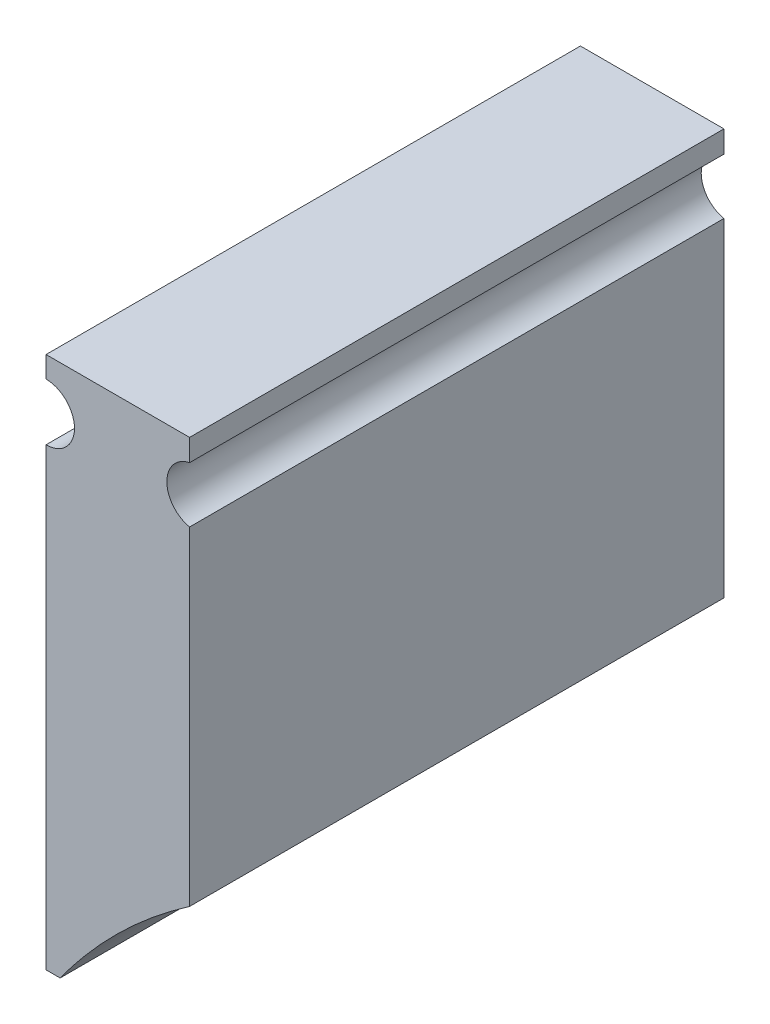
SolidWorks part; units mm, degrees
ref_plane "Plan de face" through (0, 0, 0) normal (0, 0, 1) x (1, 0, 0)
ref_plane "Plan de dessus" through (0, 0, 0) normal (0, 1, 0) x (1, 0, 0)
ref_plane "Plan de droite" through (0, 0, 0) normal (1, 0, 0) x (0, 0, -1)
sketch "Esquisse1" plane through (0, 0, 0) normal (0, 1, 0) x (1, 0, 0)
  line L1 (-2.667, 19.304) -> (2.4638, 19.304)
  line L2 (-2.667, 19.304) -> (-2.667, 0.2032)
  line L3 (-2.667, 0.2032) -> (2.4638, 0.2032)
  line L4 (2.4638, 19.304) -> (2.4638, 0.2032)
  point P4 (0, 0)
  dimension "D1" = 5.1308
  dimension "D2" = 19.1008
extrude "Boss.-Extru.1" add sketch "Esquisse1" along normal blind 19.05
sketch "Esquisse2" plane through (0, 0, 0) normal (0, 0, 1) x (1, 0, 0)
  line L0 (2.4638, 4.5293) -> (2.4638, 0)
  line L1 (2.4638, 0) -> (-2.1642, 0)
  line L2 (2.4638, 19.05) -> (2.4638, 0) construction
  line L3 (-2.667, 0) -> (2.4638, 0) construction
  spline S0 degree 2 poles (-2.1642, 0) (-0.2356, 2.6631) (2.4638, 4.5293) knots 0 0 0 1 1 1
  point P3 (0, 0)
  point P5 (0, 0)
  point P6 (0, 0)
  point P7 (0, 0)
  point P10 (0, 0)
  point P13 (2.4638, 7.2539)
  point P14 (-0.451, 3.7981)
  point P15 (2.4638, 5.0648)
  point P16 (2.3881, 5.0648)
  point P17 (-2.1616, 0.1546)
  point P20 (2.4638, 4.6062)
  point P21 (1.2743, 3.6671)
  point P22 (2.4638, 4.2017)
  point P23 (2.4638, 4.7476)
  point P24 (0.8812, 3.9833)
  point P25 (2.4638, 4.5293)
  point P26 (0.1168, 2.6183)
extrude "Enlèv. mat.-Extru.1" cut sketch "Esquisse2" against normal through all
sketch "Esquisse3" plane through (0, 0, 0) normal (0, 0, 1) x (1, 0, 0)
  line L0 (-2.667, 19.05) -> (-2.667, 0) construction
  line L1 (-2.667, 19.05) -> (2.4638, 19.05) construction
  line L2 (-2.667, 18.288) -> (-2.667, 16.256)
  arc A0 (-2.667, 18.288) -> (-2.667, 16.256) centre (-2.667, 17.272) cw
  point P3 (0, 0)
  point P4 (0, 0)
  dimension "D1" = 2.794
  dimension "D2" = 0.762
extrude "Enlèv. mat.-Extru.2" cut sketch "Esquisse3" against normal through all
mirror "Symétrie1" about plane through (0, 0, 0) normal (1, 0, 0) of "Enlèv. mat.-Extru.2"
